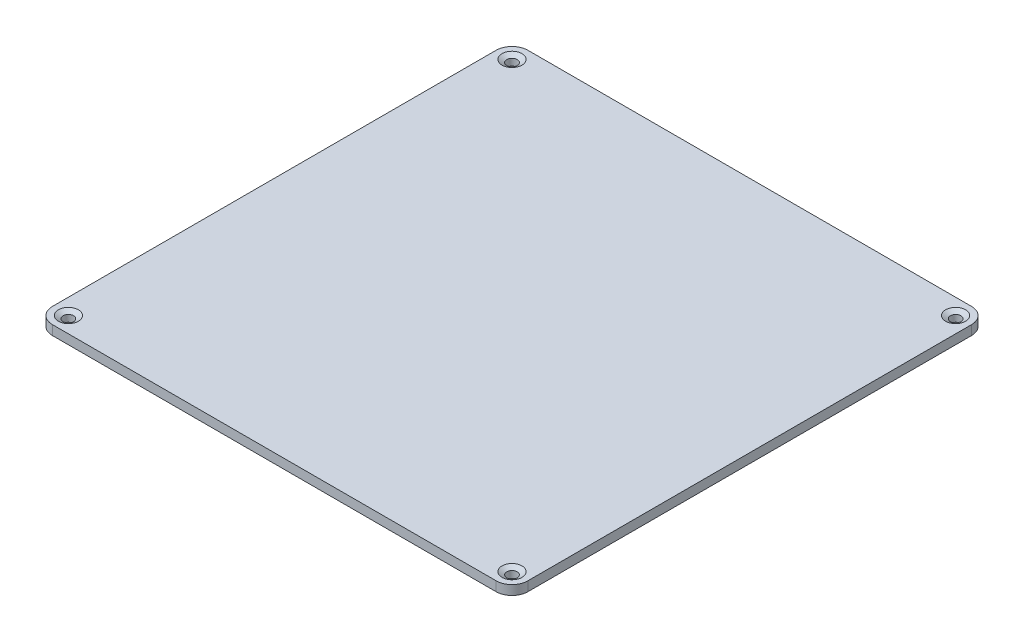
SolidWorks part; units mm, degrees
ref_plane "Front Plane" through (0, 0, 0) normal (0, 0, 1) x (1, 0, 0)
ref_plane "Top Plane" through (0, 0, 0) normal (0, 1, 0) x (1, 0, 0)
ref_plane "Right Plane" through (0, 0, 0) normal (1, 0, 0) x (0, 0, -1)
sketch "Sketch1" plane through (0, 0, 0) normal (0, 1, 0) x (1, 0, 0)
  line L1 (-75, -75) -> (75, -75)
  line L2 (-75, -75) -> (-75, 75)
  line L3 (-75, 75) -> (75, 75)
  line L4 (75, -75) -> (75, 75)
  line L5 (-75, -75) -> (75, 75) construction
  line L6 (-75, 75) -> (75, -75) construction
  point P0 (0, 0)
  dimension "D1" = 150
  dimension "D2" = 150
extrude "Boss-Extrude1" add sketch "Sketch1" along normal blind 3
sketch "Sketch2" plane through (0, 3, 0) normal (0, 1, 0) x (1, 0, 0)
  line L0 (-75, 0) -> (75, 0) construction
  line L1 (-75, 75) -> (-75, -75) construction
  line L2 (75, -75) -> (75, 75) construction
  line L3 (0, 75) -> (0, -75) construction
  line L4 (75, 75) -> (-75, 75) construction
  line L5 (-75, -75) -> (75, -75) construction
  circle A0 centre (-70, 70) radius 1.65
  circle A1 centre (70, 70) radius 1.65
  circle A2 centre (70, -70) radius 1.65
  circle A3 centre (-70, -70) radius 1.65
  dimension "D1" = 3.3
  dimension "D2" = 70
  dimension "D3" = 70
extrude "Cut-Extrude1" cut sketch "Sketch2" against normal up to next
chamfer "Chamfer1" distance 1.5 angle 30 4 edges at (70, 3, 71.65) (-70, 3, 68.35) (70, 3, -71.65) (-70, 3, -68.35)
fillet "Fillet1" radius 5 4 edges at (-75, 1.5, 75) (75, 1.5, 75) (75, 1.5, -75) (-75, 1.5, -75)
